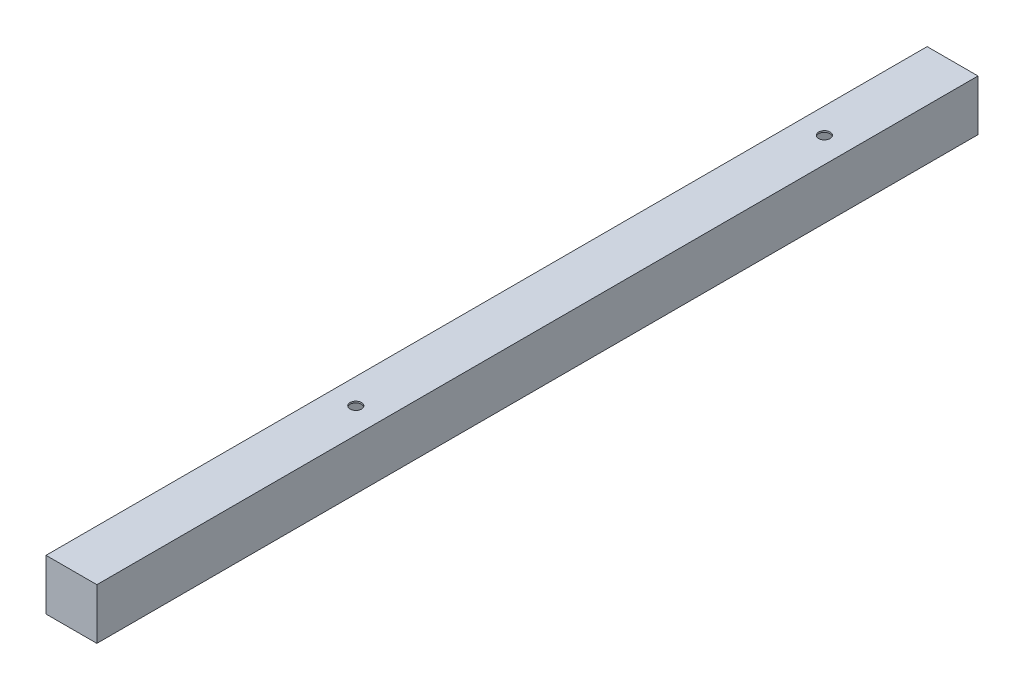
SolidWorks part; units mm, degrees
ref_plane "Alzado" through (0, 0, 0) normal (0, 0, 1) x (1, 0, 0)
ref_plane "Planta" through (0, 0, 0) normal (0, 1, 0) x (1, 0, 0)
ref_plane "Vista lateral" through (0, 0, 0) normal (1, 0, 0) x (0, 0, -1)
sketch "Croquis1" plane through (0, 0, 0) normal (0, 0, 1) x (1, 0, 0)
  line L0 (1.9, -1.9) -> (61.6, -1.9)
  line L1 (0, 0) -> (63.5, 0)
  line L2 (0, 0) -> (0, -63.5)
  line L3 (0, -63.5) -> (63.5, -63.5)
  line L4 (63.5, 0) -> (63.5, -63.5)
  line L5 (61.6, -1.9) -> (61.6, -61.6)
  line L6 (1.9, -61.6) -> (61.6, -61.6)
  line L7 (1.9, -1.9) -> (1.9, -61.6)
  dimension "D1" = 63.5
  dimension "D2" = 63.5
  dimension "D3" = 1.9
extrude "Saliente-Extruir1" add sketch "Croquis1" along normal blind 1100
sketch "Croquis2" plane through (0, 0, 1100) normal (0, 0, 1) x (1, 0, 0)
  line L1 (1.9, -1.9) -> (61.6, -1.9)
  line L2 (1.9, -1.9) -> (1.9, -61.6)
  line L3 (1.9, -61.6) -> (61.6, -61.6)
  line L4 (61.6, -1.9) -> (61.6, -61.6)
extrude "Saliente-Extruir2" add sketch "Croquis2" against normal blind 2
sketch "Croquis3" plane through (0, 0, 0) normal (0, 0, -1) x (-1, 0, 0)
  line L1 (-61.6, -1.9) -> (-1.9, -1.9)
  line L2 (-61.6, -1.9) -> (-61.6, -61.6)
  line L3 (-61.6, -61.6) -> (-1.9, -61.6)
  line L4 (-1.9, -1.9) -> (-1.9, -61.6)
extrude "Saliente-Extruir3" add sketch "Croquis3" against normal blind 2
sketch "Croquis4" plane through (0, 0, 0) normal (0, 1, 0) x (1, 0, 0)
  line L0 (31.75, 0) -> (31.75, -160) construction
  line L1 (63.5, 0) -> (0, 0) construction
  line L2 (31.75, -160) -> (31.75, -745) construction
  circle A0 centre (31.75, -160) radius 7.1437
  circle A1 centre (31.75, -745) radius 7.1437
  dimension "D2" = 14.2875
  dimension "D4" = 14.2875
  dimension "D1" = 160
  dimension "D3" = 585
extrude "Cortar-Extruir1" cut sketch "Croquis4" against normal blind 120
